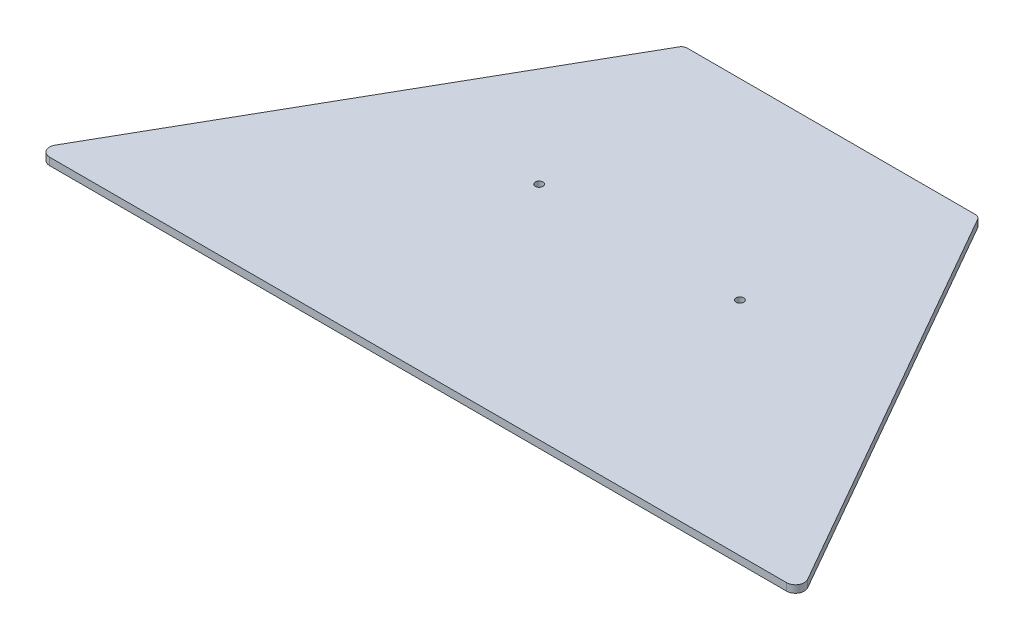
SolidWorks part; units mm, degrees
ref_plane "Front Plane" through (0, 0, 0) normal (0, 0, 1) x (1, 0, 0)
ref_plane "Top Plane" through (0, 0, 0) normal (0, 1, 0) x (1, 0, 0)
ref_plane "Right Plane" through (0, 0, 0) normal (1, 0, 0) x (0, 0, -1)
sketch "Sketch1" plane through (0, 0, 0) normal (0, 1, 0) x (1, 0, 0)
  line L0 (0, 0) -> (165.1, 0)
  line L1 (0, 177.8) -> (63.5, 177.8)
  line L2 (165.1, 0) -> (63.5, 177.8)
  line L3 (0, 177.8) -> (0, 0)
  dimension "D1" = 165.1
  dimension "D2" = 177.8
extrude "Boss-Extrude1" add sketch "Sketch1" along normal blind 3.175
mirror "Mirror1" about plane through (0, 0, 0) normal (1, 0, 0) of "Boss-Extrude1"
fillet "Fillet1" radius 3.81 2 edges at (165.1, 1.5875, 0) (-165.1, 1.5875, 0)
fillet "Fillet2" radius 2.54 2 edges at (63.5, 1.5875, -177.8) (-63.5, 1.5875, -177.8)
sketch "Sketch2" plane through (0, 3.175, 0) normal (0, 1, 0) x (1, 0, 0)
  circle A0 centre (43.18, 95.25) radius 1.651
  dimension "D1" = 3.302
  dimension "D3" = 43.18
  dimension "D2" = 95.25
extrude "Cut-Extrude1" cut sketch "Sketch2" against normal through all
mirror "Mirror2" about plane through (0, 0, 0) normal (1, 0, 0) of "Cut-Extrude1"
